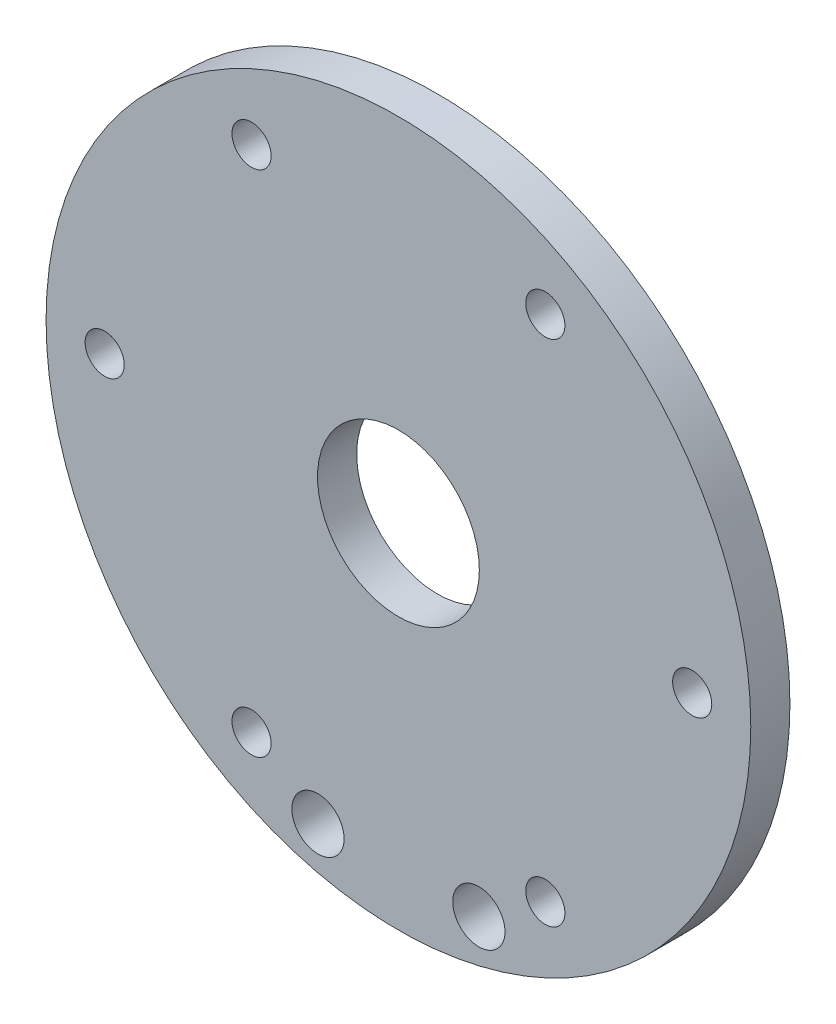
SolidWorks part; units mm, degrees
ref_plane "前视基准面" through (0, 0, 0) normal (0, 0, 1) x (1, 0, 0)
ref_plane "上视基准面" through (0, 0, 0) normal (0, 1, 0) x (1, 0, 0)
ref_plane "右视基准面" through (0, 0, 0) normal (1, 0, 0) x (0, 0, -1)
sketch "草图1" plane through (0, 0, 0) normal (0, 0, 1) x (1, 0, 0)
  circle A0 centre (3146.4172, 2145.9033) radius 6.2
  circle A1 centre (3146.4172, 2145.9033) radius 27
  circle A2 centre (3152.581, 2122.8768) radius 2
  circle A3 centre (3168.9276, 2145.9033) radius 1.5
  circle A4 centre (3157.6724, 2165.3979) radius 1.5
  circle A5 centre (3135.162, 2165.3979) radius 1.5
  circle A6 centre (3123.9068, 2145.9033) radius 1.5
  circle A7 centre (3135.162, 2126.4088) radius 1.5
  circle A8 centre (3157.6724, 2126.4088) radius 1.5
  circle A9 centre (3140.2534, 2122.8768) radius 2
extrude "凸台-拉伸1" add sketch "草图1" along normal blind 3
